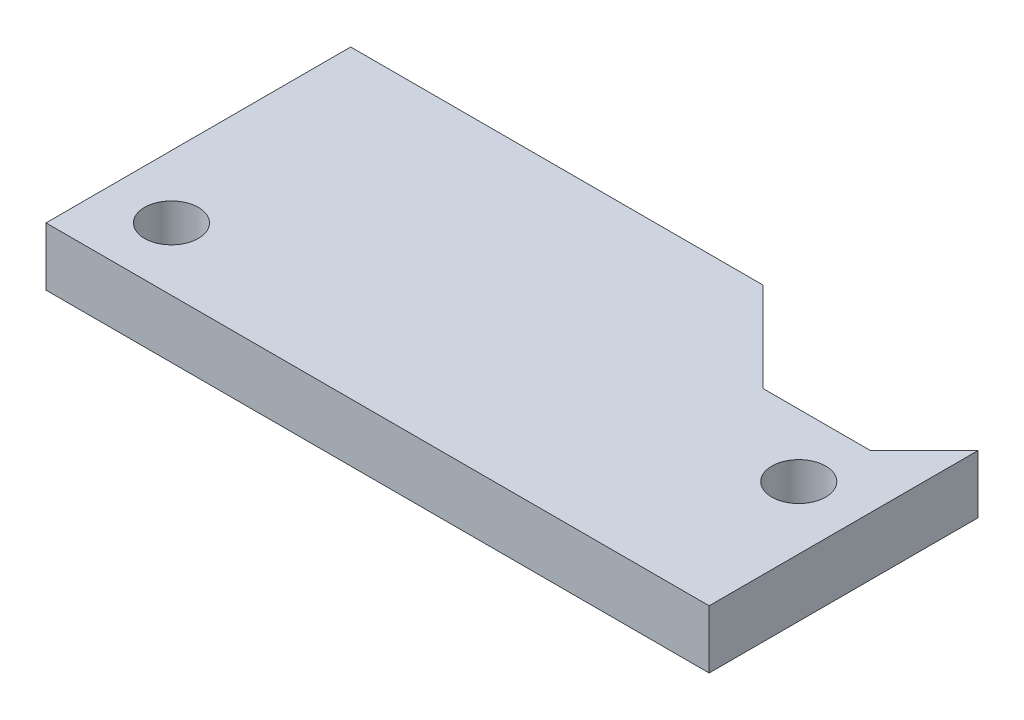
SolidWorks part; units mm, degrees
ref_plane "Front Plane" through (0, 0, 0) normal (0, 0, 1) x (1, 0, 0)
ref_plane "Top Plane" through (0, 0, 0) normal (0, 1, 0) x (1, 0, 0)
ref_plane "Right Plane" through (0, 0, 0) normal (1, 0, 0) x (0, 0, -1)
sketch "Sketch1" plane through (0, 0, 0) normal (0, 1, 0) x (1, 0, 0)
  line L0 (-18.5, 8.5) -> (18.5, -8.5) construction
  line L1 (-18.5, 8.5) -> (4.5, 8.5)
  line L2 (-18.5, 8.5) -> (-18.5, -8.5)
  line L3 (-18.5, -8.5) -> (18.5, -8.5)
  line L4 (18.5, 6.5) -> (18.5, -8.5)
  line L5 (4.5, 8.5) -> (9.5, 3.5)
  line L6 (9.5, 3.5) -> (15.5, 3.5)
  line L7 (15.5, 3.5) -> (18.5, 6.5)
  circle A0 centre (-15, -5) radius 1.5025
  circle A12 centre (15, 0) radius 1.5025
  arc A21 (9.3525, 3.6442) -> (10, 3.4975) centre (10, 5) ccw [skipped]
  arc A22 (15, 3.4975) -> (15.6475, 3.6442) centre (15, 5) ccw [skipped]
  circle A23 centre (-15, 5) radius 1.5025 [skipped]
  arc A24 (-8.8302, 4.0571) -> (-11.4774, 5.2734) centre (-10, 5) ccw [skipped]
  circle A25 centre (-5, 5) radius 1.5025 [skipped]
  circle A26 centre (0, 5) radius 1.5025 [skipped]
  circle A27 centre (5, 5) radius 1.5025 [skipped]
  circle A28 centre (-15, 0) radius 1.5025 [skipped]
  circle A29 centre (-10, 0) radius 1.5025 [skipped]
  circle A30 centre (-5, 0) radius 1.5025 [skipped]
  arc A31 (-1.3653, 0.6273) -> (1.3653, -0.6273) centre (0, 0) ccw [skipped]
  circle A32 centre (5, 0) radius 1.5025 [skipped]
  circle A33 centre (10, 0) radius 1.5025 [skipped]
  circle A34 centre (15, -5) radius 1.5025 [skipped]
  arc A35 (11.4774, -5.2734) -> (8.8302, -4.0571) centre (10, -5) ccw [skipped]
  circle A36 centre (5, -5) radius 1.5025 [skipped]
  circle A37 centre (0, -5) radius 1.5025 [skipped]
  circle A38 centre (-5, -5) radius 1.5025 [skipped]
  circle A39 centre (-10, -5) radius 1.5025 [skipped]
  dimension "D7" = 3.5
  dimension "D8" = 3.5
  dimension "D9" = 3.005
  dimension "D2" = 17
  dimension "D3" = 6
  dimension "D4" = 14
  dimension "D5" = 15
  dimension "D6" = 12
  dimension "D16" = 5
  dimension "D17" = 37
  dimension "D10" = 7
  dimension "D11" = 3
extrude "Boss-Extrude1" add sketch "Sketch1" along normal blind 3.25
